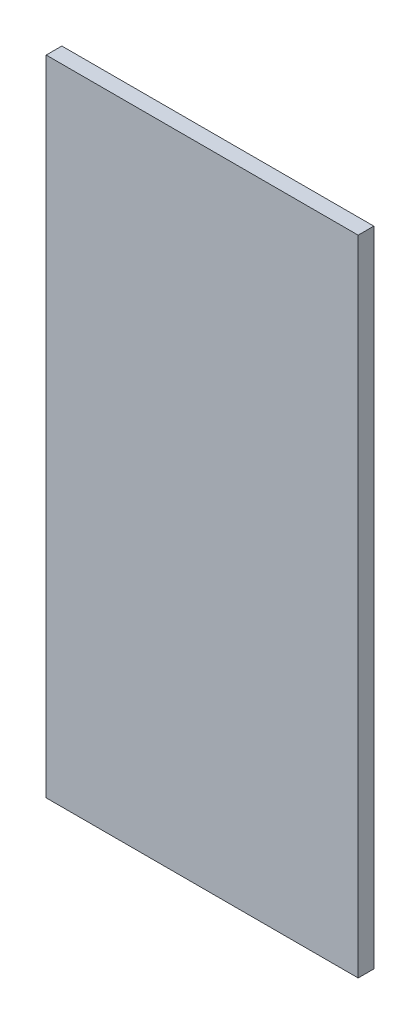
SolidWorks part; units mm, degrees
ref_plane "Front Plane" through (0, 0, 0) normal (0, 0, 1) x (1, 0, 0)
ref_plane "Top Plane" through (0, 0, 0) normal (0, 1, 0) x (1, 0, 0)
ref_plane "Right Plane" through (0, 0, 0) normal (1, 0, 0) x (0, 0, -1)
sketch "Sketch1" plane through (0, 0, 0) normal (0, 0, 1) x (1, 0, 0)
  line L1 (-57.15, 117.856) -> (57.15, 117.856)
  line L2 (-57.15, 117.856) -> (-57.15, -117.856)
  line L3 (-57.15, -117.856) -> (57.15, -117.856)
  line L4 (57.15, 117.856) -> (57.15, -117.856)
  line L5 (-57.15, 117.856) -> (57.15, -117.856) construction
  line L6 (-57.15, -117.856) -> (57.15, 117.856) construction
  point P0 (0, 0)
  dimension "D1" = 235.712
  dimension "D2" = 114.3
extrude "Boss-Extrude1" add sketch "Sketch1" along normal blind 5.7328
